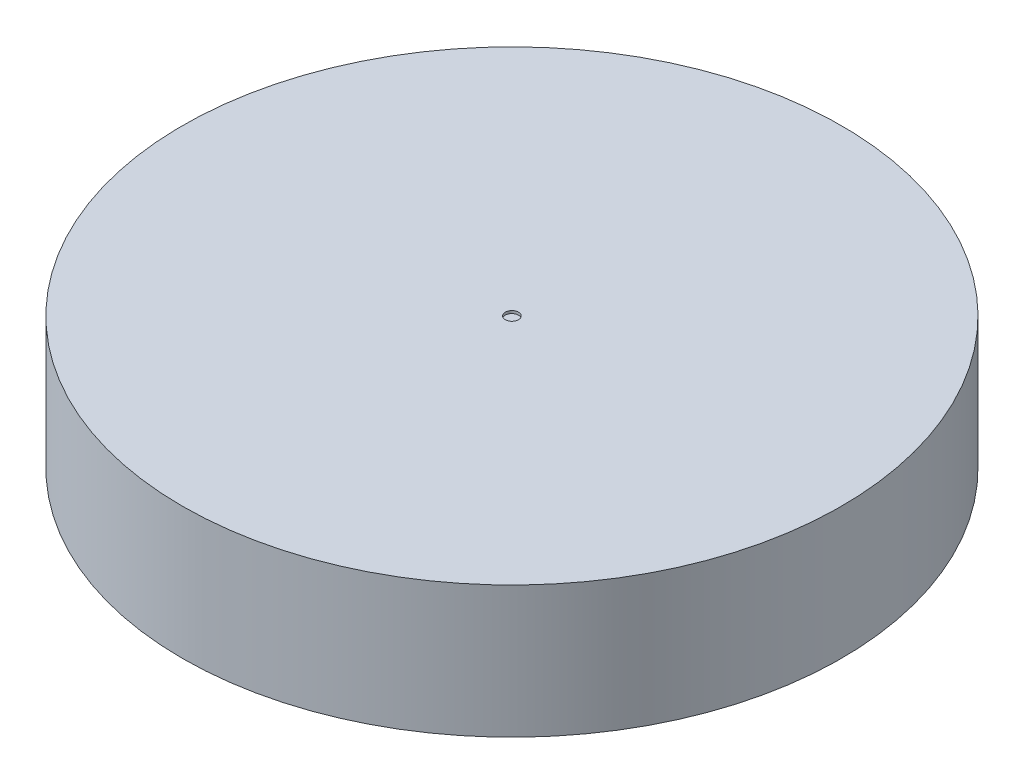
SolidWorks part; units mm, degrees
material "ABS"
ref_plane "Plano frontal" through (0, 0, 0) normal (0, 0, 1) x (1, 0, 0)
ref_plane "Plano superior" through (0, 0, 0) normal (0, 1, 0) x (1, 0, 0)
ref_plane "Plano direito" through (0, 0, 0) normal (1, 0, 0) x (0, 0, -1)
sketch "Esboço1" plane through (0, 0, 0) normal (0, 1, 0) x (1, 0, 0)
  circle A0 centre (0, 0) radius 25
  point P2 (0, 0)
  dimension "D1" = 50
extrude "Ressalto-extrusão1" add sketch "Esboço1" along normal blind 10
sketch "Esboço2" plane through (0, 0, 0) normal (0, -1, 0) x (1, 0, 0)
  line L1 (2.6, -5.1) -> (-2.6, -5.1)
  line L2 (2.6, -5.1) -> (2.6, 5.1)
  line L3 (2.6, 5.1) -> (-2.6, 5.1)
  line L4 (-2.6, -5.1) -> (-2.6, 5.1)
  line L5 (2.6, -5.1) -> (-2.6, 5.1) construction
  line L6 (2.6, 5.1) -> (-2.6, -5.1) construction
  line L7 (5.1, -2.6) -> (-5.1, -2.6)
  line L8 (5.1, -2.6) -> (5.1, 2.6)
  line L9 (5.1, 2.6) -> (-5.1, 2.6)
  line L10 (-5.1, -2.6) -> (-5.1, 2.6)
  line L11 (5.1, -2.6) -> (-5.1, 2.6) construction
  line L12 (5.1, 2.6) -> (-5.1, -2.6) construction
  point P0 (0, 0)
  point P5 (0, 0)
  point P7 (0, 0)
  dimension "D1" = 10.2
  dimension "D2" = 5.2
  dimension "D3" = 10.2
  dimension "D4" = 5.2
extrude "Corte-extrusão1" cut sketch "Esboço2" against normal blind 6 contours L10 L7 L4 L9 | L2 L9 L4 L7 | L9 L2 L3 L4 | L8 L9 L2 L7 | L2 L7 L4 L1
sketch "Esboço3" plane through (0, 10, 0) normal (0, 1, 0) x (1, 0, 0)
  circle A0 centre (0, 0) radius 0.5
  point P2 (0, 0)
  dimension "D1" = 1
extrude "Corte-extrusão2" cut sketch "Esboço3" against normal blind 0.2
